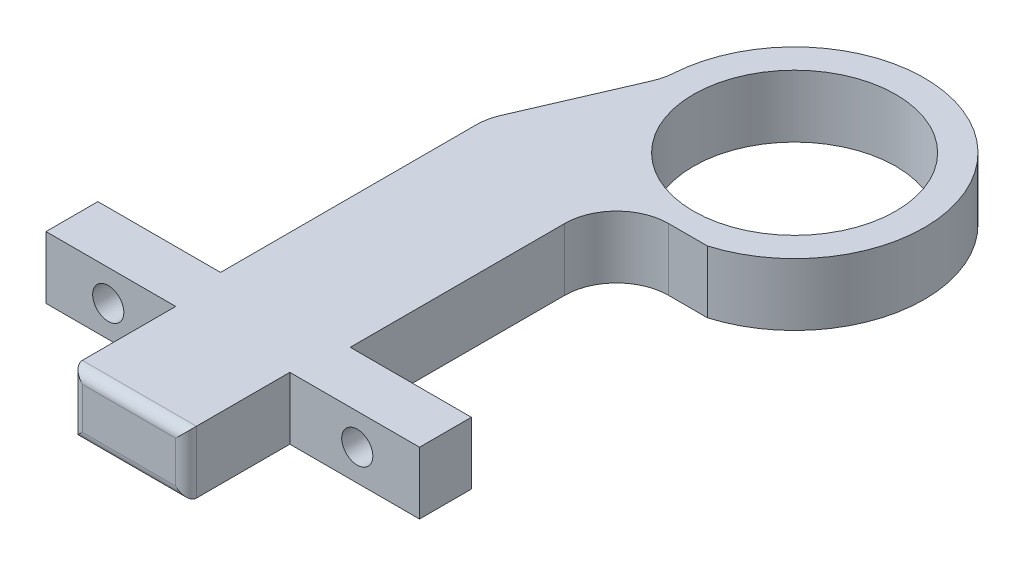
SolidWorks part; units mm, degrees
ref_plane "Alzado" through (0, 0, 0) normal (0, 0, 1) x (1, 0, 0)
ref_plane "Planta" through (0, 0, 0) normal (0, 1, 0) x (1, 0, 0)
ref_plane "Vista lateral" through (0, 0, 0) normal (1, 0, 0) x (0, 0, -1)
sketch "Croquis1" plane through (0, 0, 0) normal (0, 1, 0) x (1, 0, 0)
  line L0 (-12.5, 0) -> (-53.5222, 0) construction
  line L1 (0, 0) -> (-12.5, 21.6506) construction
  line L2 (-29.7673, 10.6211) -> (-25.3747, 20.7837)
  line L3 (-24, -31) -> (-24, -21) construction
  line L4 (-30.1777, -21) -> (-17.6777, -21)
  line L8 (-29.5, -21) -> (-18.5, -21)
  line L9 (-29.5, -21) -> (-29.5, -31)
  line L10 (-29.5, -31) -> (-18.5, -31)
  line L11 (-18.5, -21) -> (-18.5, -31)
  line L12 (-42, -16) -> (-27, -16) construction
  line L13 (-10.5, -16) -> (-6, -16) construction
  line L14 (-42, -16) -> (-27, -16)
  line L15 (-42, -16) -> (-42, -21)
  line L16 (-42, -21) -> (-30.1777, -21)
  line L18 (-6, -16) -> (-10.5, -16)
  line L19 (-6, -16) -> (-6, -21)
  line L20 (-6, -21) -> (-17.6777, -21)
  line L21 (-17.6777, -16) -> (-30.1777, -16)
  line L22 (-17.6777, -16) -> (-17.6777, 4.6717)
  line L23 (-17.6777, 9.6717) -> (-30.1777, 9.6717)
  line L24 (-30.1777, -16) -> (-30.1777, 8.6374)
  line L25 (-8.9286, 9.6717) -> (-12.6777, 9.6717)
  line L26 (-10.5, -16) -> (-17.6777, -16)
  arc A1 (-8.9286, 9.6717) -> (-24.9745, 22.4484) centre (-12.5, 21.6506) ccw
  circle A2 centre (-12.5, 21.6506) radius 9.75
  arc A6 (-30.1777, 8.6374) -> (-29.7673, 10.6211) centre (-25.1777, 8.6374) cw
  arc A7 (-24.9745, 22.4484) -> (-25.3747, 20.7837) centre (-29.9643, 22.7675) cw
  arc A8 (-17.6777, 4.6717) -> (-12.6777, 9.6717) centre (-12.6777, 4.6717) cw
  point P31 (-25, 21.6506)
  dimension "D3" = 25
  dimension "D4" = 5
  dimension "D5" = 19.5
  dimension "D6" = 21
  dimension "D1" = 25
  dimension "D2" = 60
  dimension "D7" = 11
  dimension "D8" = 10
  dimension "D9" = 24
  dimension "D10" = 5
  dimension "D11" = 18
  dimension "D12" = 18
extrude "Saliente-Extruir1" add sketch "Croquis1" along normal blind 6
sketch "Croquis2" plane through (0, 0, 21) normal (0, 0, 1) x (1, 0, 0)
  line L0 (-42, 3) -> (-6, 3) construction
  line L1 (-42, 6) -> (-42, 0) construction
  line L2 (-6, 6) -> (-6, 0) construction
  line L3 (-24, 6) -> (-24, 0) construction
  line L4 (-29.5, 6) -> (-18.5, 6) construction
  line L5 (-29.5, 0) -> (-18.5, 0) construction
  circle A0 centre (-36, 3) radius 1.5
  circle A1 centre (-12, 3) radius 1.5
  dimension "D3" = 3
  dimension "D4" = 3
  dimension "D1" = 12
  dimension "D2" = 12
extrude "Cortar-Extruir1" cut sketch "Croquis2" against normal blind 6
fillet "Redondeo1" radius 1 4 edges at (-29.5, 3, 31) (-18.5, 3, 31) (-24, 6, 31) (-24, 0, 31)
